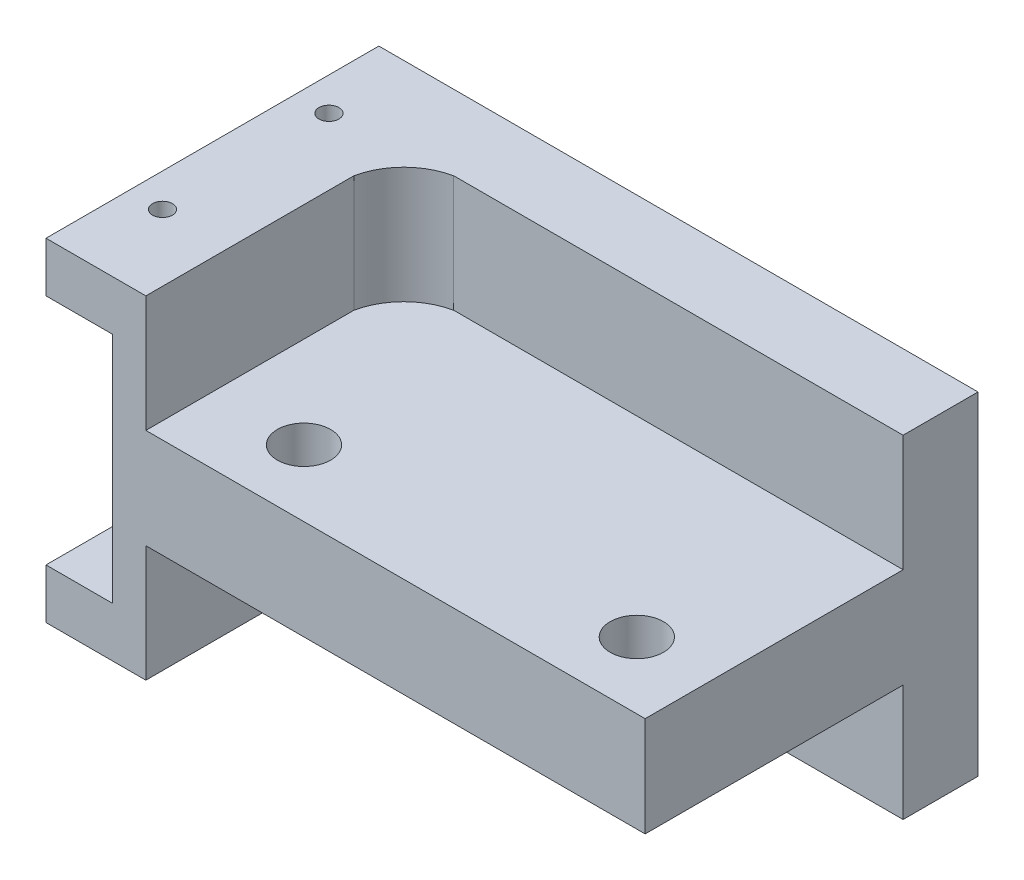
SolidWorks part; units mm, degrees
ref_plane "Front Plane" through (0, 0, 0) normal (0, 0, 1) x (1, 0, 0)
ref_plane "Top Plane" through (0, 0, 0) normal (0, 1, 0) x (1, 0, 0)
ref_plane "Right Plane" through (0, 0, 0) normal (1, 0, 0) x (0, 0, -1)
sketch "Sketch1" plane through (0, 0, 0) normal (0, 1, 0) x (1, 0, 0)
  line L1 (-17.5, -10) -> (17.5, -10)
  line L2 (-17.5, -10) -> (-17.5, 10)
  line L3 (-17.5, 10) -> (17.5, 10)
  line L4 (17.5, -10) -> (17.5, 10)
  point P0 (0, 0)
  dimension "D1" = 20
  dimension "D2" = 35
extrude "Boss-Extrude2" add sketch "Sketch1" along normal mid plane 20
sketch "Sketch4" plane through (0, 10, 0) normal (0, 1, 0) x (1, 0, 0)
  line L0 (-12.5, -10) -> (-12.5, 2.5)
  line L1 (-17.5, -10) -> (17.5, -10) construction
  line L2 (-9.5, 5.5) -> (17.5, 5.5)
  line L3 (17.5, -10) -> (17.5, 10) construction
  line L4 (17.5, 5.5) -> (17.5, -10)
  line L5 (17.5, -10) -> (-12.5, -10)
  line L6 (17.5, -10) -> (17.5, 10) construction
  line L7 (-17.5, -10) -> (17.5, -10) construction
  arc A0 (-12.5, 2.5) -> (-9.5, 5.5) centre (-8.7081, 1.7081) cw
  dimension "D1" = 5
  dimension "D2" = 4.5
extrude "Cut-Extrude1" cut sketch "Sketch4" against normal blind 7
sketch "Sketch6" plane through (0, -10, 0) normal (0, -1, 0) x (1, 0, 0)
  line L0 (-12.5, 10) -> (-12.5, -2.5)
  line L1 (-17.5, 10) -> (17.5, 10) construction
  line L2 (-9.5, -5.5) -> (17.5, -5.5)
  line L3 (17.5, 10) -> (17.5, -10) construction
  line L8 (-12.5, 10) -> (17.5, 10)
  line L9 (17.5, 10) -> (17.5, -5.5)
  arc A0 (-12.5, -2.5) -> (-9.5, -5.5) centre (-9.1347, -2.1347) ccw
extrude "Cut-Extrude2" cut sketch "Sketch6" against normal blind 7
sketch "Sketch8" plane through (0, 3, 0) normal (0, 1, 0) x (1, 0, 0)
  line L0 (-12.5, -10) -> (17.5, -10) construction
  line L1 (-12.5, 2.5) -> (-12.5, -10) construction
  line L2 (17.5, -10) -> (17.5, 5.5) construction
  circle A0 centre (-7, -6) radius 1.6
  circle A1 centre (13, -6) radius 1.6
  dimension "D1" = 3.2
  dimension "D2" = 3.2
  dimension "D3" = 4
  dimension "D4" = 5.5
  dimension "D5" = 0
  dimension "D6" = 20
  dimension "D7" = 4.5
extrude "Cut-Extrude3" cut sketch "Sketch8" against normal blind 7
sketch "Sketch9" plane through (-17.5, 0, 0) normal (-1, 0, 0) x (0, 0, 1)
  line L0 (-10, 10) -> (-10, -10) construction
  line L1 (-10, 7) -> (10, 7)
  line L2 (-10, 7) -> (-10, -7)
  line L3 (-10, -7) -> (10, -7)
  line L4 (10, 7) -> (10, -7)
  line L5 (10, 10) -> (10, -10) construction
  line L6 (-10, 10) -> (10, 10) construction
  line L7 (-10, -10) -> (10, -10) construction
  dimension "D1" = 3
  dimension "D2" = 3
  dimension "D3" = 14
extrude "Cut-Extrude4" cut sketch "Sketch9" against normal blind 3
sketch "Sketch10" plane through (0, 10, 0) normal (0, 1, 0) x (1, 0, 0)
  line L0 (17.5, 10) -> (-17.5, 10) construction
  line L1 (-17.5, 10) -> (-17.5, -10) construction
  circle A0 centre (-16.5, 5) radius 0.6
  circle A1 centre (-16.5, -5) radius 0.6
  dimension "D1" = 1.2
  dimension "D2" = 1.2
  dimension "D3" = 10
  dimension "D4" = 5
  dimension "D5" = 1
  dimension "D6" = 1
extrude "Cut-Extrude5" cut sketch "Sketch10" against normal blind 3
sketch "Sketch11" plane through (0, -10, 0) normal (0, -1, 0) x (1, 0, 0)
  line L0 (-17.5, -10) -> (-17.5, 10) construction
  line L1 (17.5, -10) -> (-17.5, -10) construction
  circle A0 centre (-16.5, 5) radius 0.6
  circle A1 centre (-16.5, -5) radius 0.6
  dimension "D1" = 1.2
  dimension "D2" = 1.2
  dimension "D3" = 1
  dimension "D4" = 1
  dimension "D5" = 10
  dimension "D6" = 5
extrude "Cut-Extrude6" cut sketch "Sketch11" against normal blind 3
sketch "Sketch12" plane through (-17.5, 0, 0) normal (-1, 0, 0) x (0, 0, 1)
  line L1 (-10, 10) -> (10, 10)
  line L2 (-10, 10) -> (-10, 7)
  line L3 (-10, 7) -> (10, 7)
  line L4 (10, 10) -> (10, 7)
extrude "Boss-Extrude3" add sketch "Sketch12" along normal blind 1
sketch "Sketch13" plane through (-17.5, 0, 0) normal (-1, 0, 0) x (0, 0, 1)
  line L1 (-10, -7) -> (10, -7)
  line L2 (-10, -7) -> (-10, -10)
  line L3 (-10, -10) -> (10, -10)
  line L4 (10, -7) -> (10, -10)
extrude "Boss-Extrude4" add sketch "Sketch13" along normal blind 1
